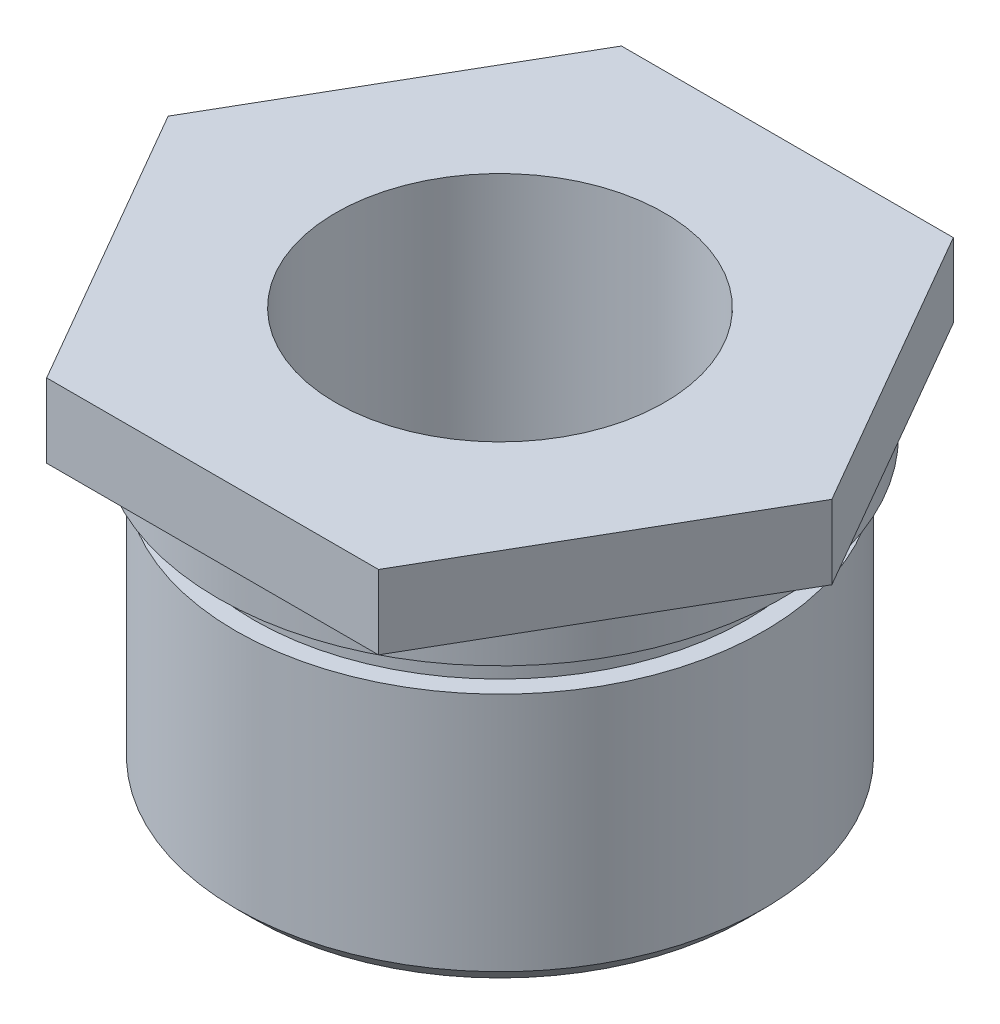
SolidWorks part; units mm, degrees
material "Brass"
ref_plane "Front" through (0, 0, 0) normal (0, 0, 1) x (1, 0, 0)
ref_plane "Top" through (0, 0, 0) normal (0, 1, 0) x (1, 0, 0)
ref_plane "Right" through (0, 0, 0) normal (1, 0, 0) x (0, 0, -1)
sketch "Sketch1" plane through (0, 0, 0) normal (1, 0, 0) x (0, 0, -1)
  line L0 (0, 13.8546) -> (0, -13.6877) construction
  line L1 (4.445, 5.5) -> (4.445, -5.5)
  line L2 (4.445, -5.5) -> (7.1437, -5.5)
  line L3 (7.1437, -5.5) -> (7.1437, 1.5)
  line L4 (7.1437, 1.5) -> (6.6437, 1.5)
  line L5 (6.6437, 1.5) -> (6.6437, 2.5)
  line L6 (6.6437, 2.5) -> (7.62, 2.5)
  line L7 (7.62, 2.5) -> (7.62, 5.5)
  line L8 (7.62, 5.5) -> (4.445, 5.5)
  line L10 (4.445, 5.5) -> (0, 5.5)
  line L11 (4.445, 5.5) -> (4.445, -5.5)
  line L12 (4.445, -5.5) -> (0, -5.5)
  line L13 (0, 5.5) -> (0, -5.5)
  point P5 (4.445, 0)
revolve "Revolve1" add sketch "Sketch1" angle 360 about L0
cosmetic thread "Cosmetic Thread1" parameters "D2"=11.7678
cosmetic thread "Cosmetic Thread2" parameters "D2"=9.144
sketch "Sketch2" plane through (0, 5.5, 0) normal (0, 1, 0) x (1, 0, 0)
  line L1 (-8.9748, 0) -> (-4.4874, -7.7724)
  line L2 (-4.4874, -7.7724) -> (4.4874, -7.7724)
  line L3 (4.4874, -7.7724) -> (8.9748, 0)
  line L4 (8.9748, 0) -> (4.4874, 7.7724)
  line L5 (4.4874, 7.7724) -> (-4.4874, 7.7724)
  line L6 (-4.4874, 7.7724) -> (-8.9748, 0)
  circle A0 centre (0, 0) radius 7.7724 construction
  circle A2 centre (0, 0) radius 4.445 construction
  circle A3 centre (0, 0) radius 4.445
  circle A5 centre (0, 0) radius 7.62
  circle A6 centre (0, 0) radius 7.62
  circle M1 centre (0, 0) radius 4.445
  circle M2 centre (0, 0) radius 7.62
extrude "Boss-Extrude1" add sketch "Sketch2" against normal blind 2 contours M2 M1 | L5 L6 L1 L2 L3 L4 M2
chamfer "Chamfer1" distance 0.5 angle 45 1 edges at (0, -5.5, 7.1437)
equation "\"D2@Sketch1\"=25.4*9/16/2"
equation "\"D4@Sketch1\"=.6*25.4/2"
equation "\"D3@Sketch1\"=.35*25.4/2"
equation "\"D1@Sketch2\"=.612*25.4"
